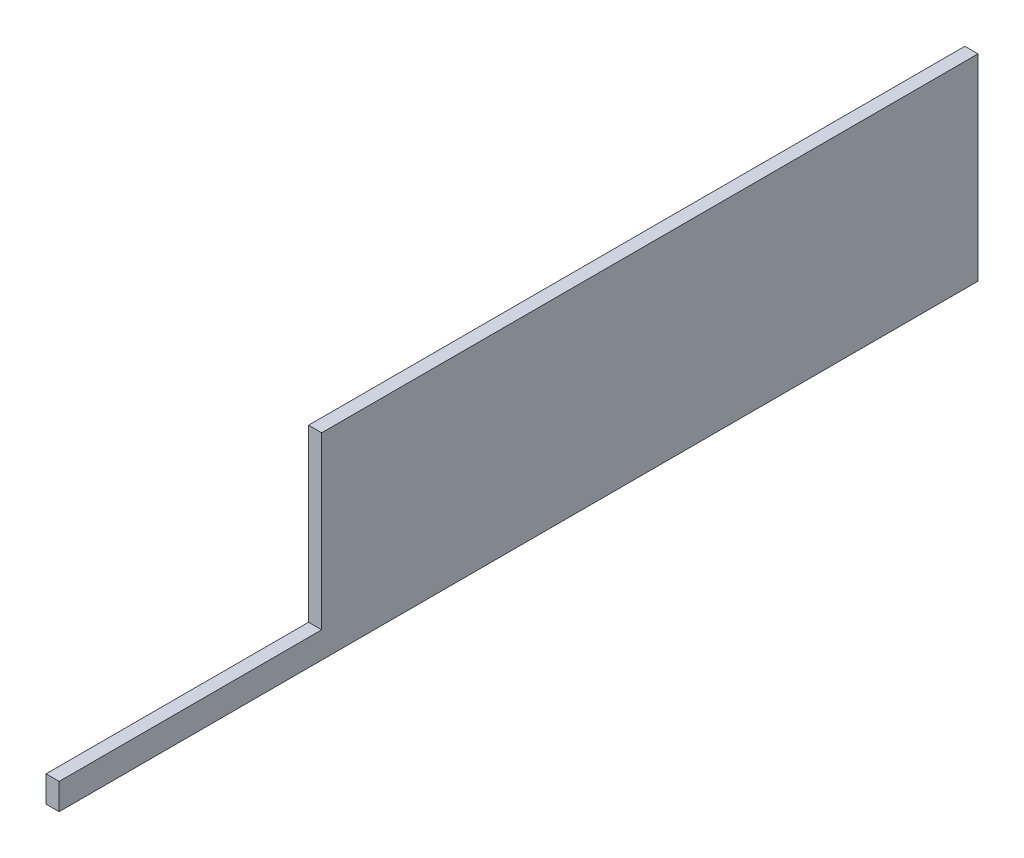
SolidWorks part; units mm, degrees
material "AISI 1020"
ref_plane "Alzado" through (0, 0, 0) normal (0, 0, 1) x (1, 0, 0)
ref_plane "Planta" through (0, 0, 0) normal (0, 1, 0) x (1, 0, 0)
ref_plane "Vista lateral" through (0, 0, 0) normal (1, 0, 0) x (0, 0, -1)
sketch "Croquis1" plane through (0, 0, 0) normal (1, 0, 0) x (0, 0, -1)
  line L1 (-25, -7.5) -> (25, -7.5)
  line L2 (-25, -7.5) -> (-25, 7.5)
  line L3 (-25, 7.5) -> (25, 7.5)
  line L4 (25, -7.5) -> (25, 7.5)
  line L5 (-25, -7.5) -> (25, 7.5) construction
  line L6 (-25, 7.5) -> (25, -7.5) construction
  line L7 (-25, -7.5) -> (-45, -7.5)
  line L8 (-25, -7.5) -> (-25, -5.5)
  line L9 (-25, -5.5) -> (-45, -5.5)
  line L10 (-45, -7.5) -> (-45, -5.5)
  point P0 (0, 0)
  dimension "D1" = 15
  dimension "D2" = 50
  dimension "D3" = 2
  dimension "D4" = 20
extrude "Saliente-Extruir1" add sketch "Croquis1" along normal blind 1 contours L10 L7 L2 L9 | L1 L4 L3 L2
